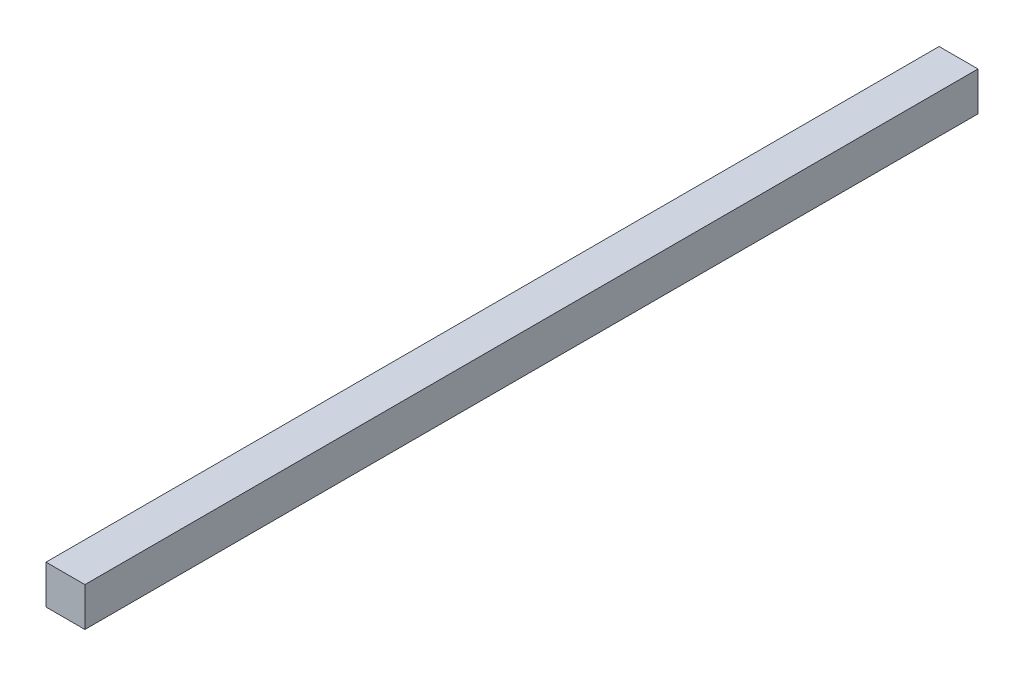
SolidWorks part; units mm, degrees
ref_plane "Front Plane" through (0, 0, 0) normal (0, 0, 1) x (1, 0, 0)
ref_plane "Top Plane" through (0, 0, 0) normal (0, 1, 0) x (1, 0, 0)
ref_plane "Right Plane" through (0, 0, 0) normal (1, 0, 0) x (0, 0, -1)
sketch "Sketch1" plane through (0, 0, 0) normal (0, 0, 1) x (1, 0, 0)
  line L1 (5, 5) -> (-5, 5)
  line L2 (5, 5) -> (5, -5)
  line L3 (5, -5) -> (-5, -5)
  line L4 (-5, 5) -> (-5, -5)
  line L5 (5, 5) -> (-5, -5) construction
  line L6 (5, -5) -> (-5, 5) construction
  point P0 (0, 0)
  dimension "D1" = 10
extrude "Boss-Extrude1" add sketch "Sketch1" along normal blind 229.597
sketch "Sketch2" plane through (0, 0, 229.597) normal (0, 0, 1) x (1, 0, 0)
  line L0 (0, 0) -> (0, 12) construction
  point P4 (0, 0)
  dimension "D1" = 12
sketch "Sketch3" plane through (0, 0, 0) normal (0, 0, -1) x (-1, 0, 0)
  line L0 (-3.4123, -15.2092) -> (-3.1656, -13.8167) construction
  line L1 (-3.1656, -13.8167) -> (-2.9189, -12.4241) construction
  line L4 (-1.2354, -14.0633) -> (-0.1851, -14.0633)
  line L5 (0, 0) -> (0, -12) construction
  line L6 (-1.7731, -14.0633) -> (-3.4123, -15.2092)
  line L7 (-1.7731, -14.0633) -> (-2.9189, -12.4241)
  line L8 (-0.7103, -13.5382) -> (-0.7103, -14.5885)
  circle A1 centre (0, 0) radius 12
  arc A2 (-10.3813, -9.6514) -> (-1.7731, -14.0633) centre (0, 0) ccw
  point P0 (0, 0)
  point P7 (0, 0)
  point P16 (-0.7103, -14.0633)
  dimension "D1" = 24
  dimension "D2" = 2
sketch "Sketch4" plane through (0, -5, 0) normal (0, -1, 0) x (-1, 0, 0)
  line L0 (0, -229.597) -> (0, -224.597)
  line L1 (5, -229.597) -> (-5, -229.597) construction
  dimension "D1" = 5
